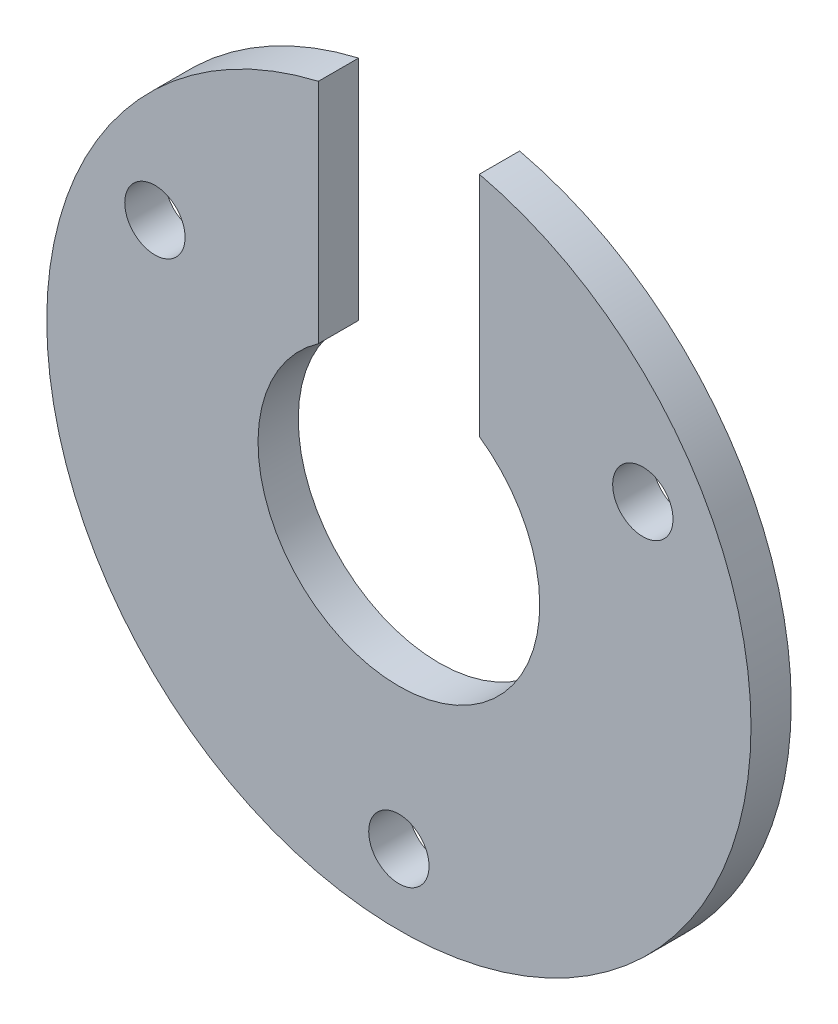
SolidWorks part; units mm, degrees
ref_plane "Front Plane" through (0, 0, 0) normal (0, 0, 1) x (1, 0, 0)
ref_plane "Top Plane" through (0, 0, 0) normal (0, 1, 0) x (1, 0, 0)
ref_plane "Right Plane" through (0, 0, 0) normal (1, 0, 0) x (0, 0, -1)
sketch "Sketch1" plane through (0, 0, 0) normal (0, 0, 1) x (1, 0, 0)
  circle A0 centre (0, 0) radius 17.5
  circle A1 centre (0, 0) radius 7
  dimension "D1" = 35
  dimension "D2" = 14
extrude "Extrude1" add sketch "Sketch1" along normal blind 2
sketch "Sketch2" plane through (0, 0, 2) normal (0, 0, 1) x (1, 0, 0)
  line L0 (0, 3.216) -> (0, 0) construction
  line L1 (-4, 3.216) -> (4, 3.216)
  line L2 (-4, 3.216) -> (-4, 19.7835)
  line L3 (-4, 19.7835) -> (4, 19.7835)
  line L4 (4, 3.216) -> (4, 19.7835)
  dimension "D1" = 8
extrude "Cut-Extrude1" cut sketch "Sketch2" against normal blind 2
hole_wizard "Ø3.0 (3) Diameter Hole1" positions "3DSketch1" profile "Sketch4" hole size "Ø3.0" standard "DIN" end condition through all
sketch3d "3DSketch1"
  line L0 (0, 0, 0) -> (0, -14, 0) construction
  line L1 (-12.1244, 7, 0) -> (0, 0, 0) construction
  line L2 (0, 0, 0) -> (12.1244, 7, 0) construction
  point P14 (0, -14, 0)
  point P16 (-12.1244, 7, 0)
  point P18 (12.1244, 7, 0)
  dimension "D1" = 14
  dimension "D2" = 14
  dimension "D3" = 14
  dimension "D4" = 120
  dimension "D5" = 120
sketch "Sketch4" plane through (0, -14, 0) normal (1, 0, 0) x (0, 1, 0)
  line L0 (0, 0) -> (0, 2)
  line L1 (0, 2) -> (1.5, 2)
  line L2 (1.5, 2) -> (1.5, 0)
  line L5 (1.5, 0) -> (0, 0)
  line L11 (0, -6.35) -> (0, 107.95) construction
  dimension "Thru Hole Dia." = 3
  dimension "Thru Hole Depth" = 2
